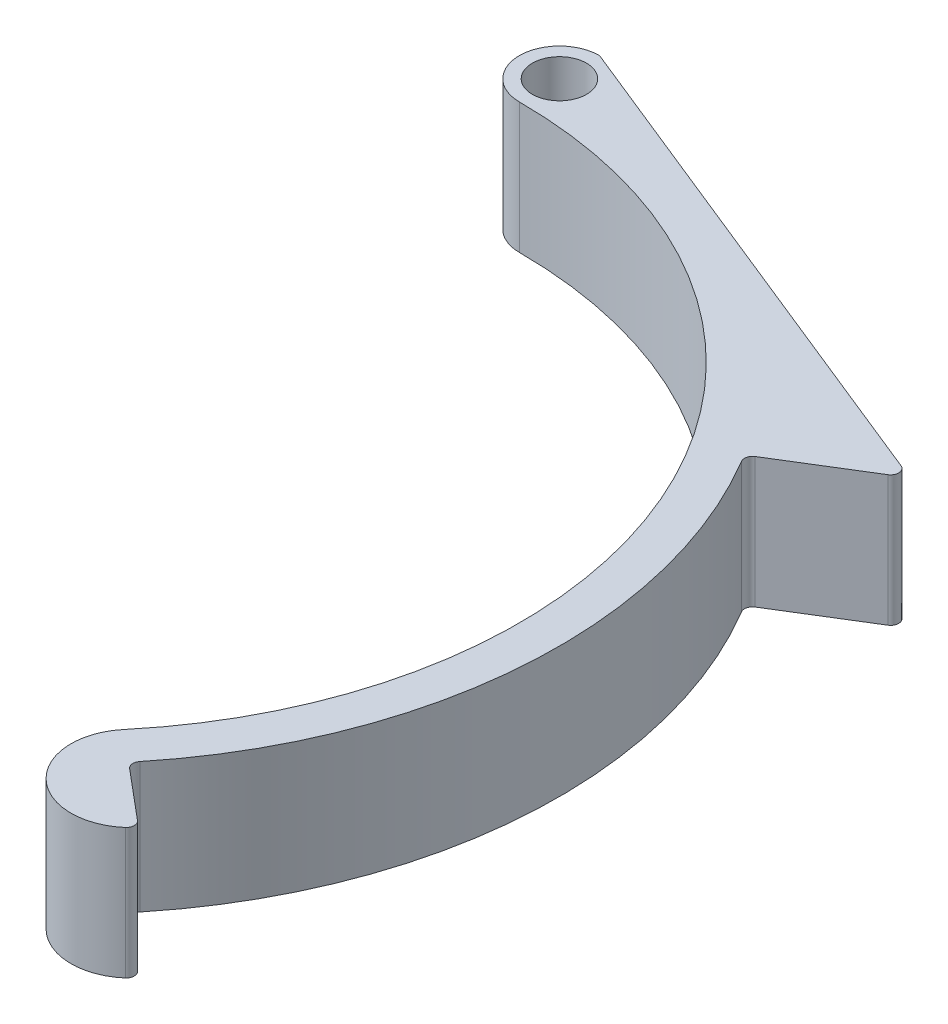
SolidWorks part; units mm, degrees
ref_plane "Front Plane" through (0, 0, 0) normal (0, 0, 1) x (1, 0, 0)
ref_plane "Top Plane" through (0, 0, 0) normal (0, 1, 0) x (1, 0, 0)
ref_plane "Right Plane" through (0, 0, 0) normal (1, 0, 0) x (0, 0, -1)
sketch "Sketch1" plane through (0, 0, 0) normal (0, 1, 0) x (1, 0, 0)
  line L0 (0, 0) -> (34.472, -28.9254) construction
  line L1 (0, 0) -> (0, -45) construction
  line L2 (0, 0) -> (63.5762, -53.3468) construction
  line L3 (0, 53) -> (51.921, 32.0189)
  line L4 (51.921, 32.0189) -> (41.707, 25.7201)
  line L5 (0, 53) -> (0, 49)
  line L7 (0, 49) -> (0, 53)
  line L8 (43.6645, -36.6389) -> (37.5362, -31.4966)
  circle A0 centre (0, 0) radius 45 construction
  arc A1 (0, 45) -> (34.472, -28.9254) centre (0, 0) cw
  arc A2 (0, 45) -> (0, 53) centre (0, 49) cw
  arc A4 (37.5362, -31.4966) -> (0, 49) centre (0, 0) ccw
  circle A5 centre (0, 49) radius 2.7
  arc A6 (41.707, 25.7201) -> (0, 49) centre (0, 0) ccw
  arc A7 (34.472, -28.9254) -> (43.6645, -36.6389) centre (39.0683, -32.7822) ccw
  dimension "D1" = 90
  dimension "D5" = 56
  dimension "D6" = 5.4
  dimension "D2" = 50
  dimension "D3" = 8
  dimension "D4" = 4
  dimension "D7" = 12
  dimension "D8" = 12
extrude "Boss-Extrude1" add sketch "Sketch1" along normal blind 13
fillet "Fillet1" radius 0.8 5 edges at (0, 6.5, -53) (51.921, 6.5, -32.0189) (41.707, 6.5, -25.7201) (43.6645, 6.5, 36.6389) (37.5362, 6.5, 31.4966)
